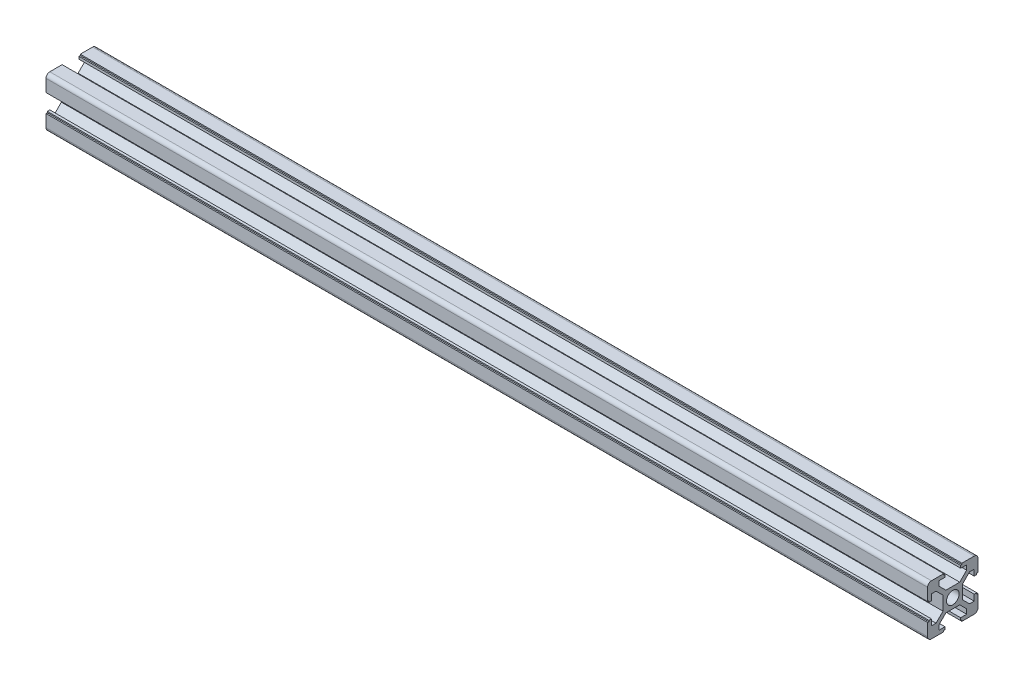
SolidWorks part; units mm, degrees
ref_plane "前视基准面" through (0, 0, 0) normal (0, 0, 1) x (1, 0, 0)
ref_plane "上视基准面" through (0, 0, 0) normal (0, 1, 0) x (1, 0, 0)
ref_plane "右视基准面" through (0, 0, 0) normal (1, 0, 0) x (0, 0, -1)
other "Configuration Table"
sketch "草图1" plane through (0, 0, 0) normal (0, 1, 0) x (1, 0, 0)
  line L0 (0, 0) -> (350, 0)
  dimension "D1" = 350
other "铝型材 20 X 20 X R1.5(1)"
ref_plane "基准面1" through (0, 0, 0) normal (1, 0, 0) x (0, 0, -1)
sketch "Sketch1" plane through (0, 0, 0) normal (1, 0, 0) x (0, 0, -1)
  line L0 (-3.6, 10) -> (-3.6, 9.5)
  line L1 (-3.6, 9.5) -> (-3.1, 9.5)
  line L2 (-3.1, 9.5) -> (-3.1, 8.5)
  line L3 (-3.1, 8.5) -> (-5.5, 8.5)
  line L4 (-8.5, -10) -> (-3.6, -10)
  line L5 (-10, -8.5) -> (-10, -3.6)
  line L6 (8.5, 10) -> (3.6, 10)
  line L7 (10, 8.5) -> (10, 3.6)
  line L8 (0, 14.8756) -> (0, 0) construction
  line L9 (0, 0) -> (14.1675, 0) construction
  line L10 (-5.5, 8.5) -> (-5.5, 6.65)
  line L11 (-5.5, 6.65) -> (-2.75, 3.9)
  line L12 (-2.75, 3.9) -> (2.75, 3.9)
  line L13 (5.5, 6.65) -> (2.75, 3.9)
  line L14 (5.5, 8.5) -> (5.5, 6.65)
  line L15 (3.1, 8.5) -> (5.5, 8.5)
  line L16 (3.1, 9.5) -> (3.1, 8.5)
  line L17 (3.6, 9.5) -> (3.1, 9.5)
  line L18 (3.6, 10) -> (3.6, 9.5)
  line L19 (-3.6, 10) -> (-8.5, 10)
  line L20 (10, 3.6) -> (9.5, 3.6)
  line L21 (9.5, 3.6) -> (9.5, 3.1)
  line L22 (9.5, 3.1) -> (8.5, 3.1)
  line L23 (8.5, 3.1) -> (8.5, 5.5)
  line L24 (8.5, 5.5) -> (6.65, 5.5)
  line L25 (6.65, 5.5) -> (3.9, 2.75)
  line L26 (3.9, 2.75) -> (3.9, -2.75)
  line L27 (6.65, -5.5) -> (3.9, -2.75)
  line L28 (8.5, -5.5) -> (6.65, -5.5)
  line L29 (8.5, -3.1) -> (8.5, -5.5)
  line L30 (9.5, -3.1) -> (8.5, -3.1)
  line L31 (9.5, -3.6) -> (9.5, -3.1)
  line L32 (10, -3.6) -> (9.5, -3.6)
  line L33 (3.6, -10) -> (3.6, -9.5)
  line L34 (3.6, -9.5) -> (3.1, -9.5)
  line L35 (3.1, -9.5) -> (3.1, -8.5)
  line L36 (3.1, -8.5) -> (5.5, -8.5)
  line L37 (5.5, -8.5) -> (5.5, -6.65)
  line L38 (5.5, -6.65) -> (2.75, -3.9)
  line L39 (2.75, -3.9) -> (-2.75, -3.9)
  line L40 (-5.5, -6.65) -> (-2.75, -3.9)
  line L41 (-5.5, -8.5) -> (-5.5, -6.65)
  line L42 (-3.1, -8.5) -> (-5.5, -8.5)
  line L43 (-3.1, -9.5) -> (-3.1, -8.5)
  line L44 (-3.6, -9.5) -> (-3.1, -9.5)
  line L45 (-3.6, -10) -> (-3.6, -9.5)
  line L46 (-10, -3.6) -> (-9.5, -3.6)
  line L47 (-9.5, -3.6) -> (-9.5, -3.1)
  line L48 (-9.5, -3.1) -> (-8.5, -3.1)
  line L49 (-8.5, -3.1) -> (-8.5, -5.5)
  line L50 (-8.5, -5.5) -> (-6.65, -5.5)
  line L51 (-6.65, -5.5) -> (-3.9, -2.75)
  line L52 (-3.9, -2.75) -> (-3.9, 2.75)
  line L53 (-6.65, 5.5) -> (-3.9, 2.75)
  line L54 (-8.5, 5.5) -> (-6.65, 5.5)
  line L55 (-8.5, 3.1) -> (-8.5, 5.5)
  line L56 (-9.5, 3.1) -> (-8.5, 3.1)
  line L57 (-9.5, 3.6) -> (-9.5, 3.1)
  line L58 (-10, 3.6) -> (-9.5, 3.6)
  line L59 (3.6, -10) -> (8.5, -10)
  line L60 (-10, 3.6) -> (-10, 8.5)
  line L61 (10, -3.6) -> (10, -8.5)
  circle A0 centre (0, 0) radius 2.5
  arc A1 (-10, 8.5) -> (-8.5, 10) centre (-8.5, 8.5) cw
  arc A2 (10, 8.5) -> (8.5, 10) centre (8.5, 8.5) ccw
  arc A3 (-8.5, -10) -> (-10, -8.5) centre (-8.5, -8.5) cw
  arc A4 (8.5, -10) -> (10, -8.5) centre (8.5, -8.5) ccw
  point P0 (-10, 0)
  point P1 (10, 0)
  point P2 (0, 10)
  point P3 (0, -10)
  point P4 (0, 0)
  point P5 (-10, -10)
  point P6 (10, -10)
  point P7 (10, 10)
  point P8 (-10, 10)
  point P13 (0, 0)
  point P36 (-10, 10)
  point P39 (10, 10)
  dimension "D1" = 11
  dimension "D2" = 20
  dimension "D3" = 6.2
  dimension "D4" = 7.2
  dimension "D5" = 6.1
  dimension "D6" = 5
  dimension "D7" = 1.5
  dimension "D8" = 45
  dimension "D9" = 0.5
  dimension "D10" = 1
  dimension "D11" = 5.5
